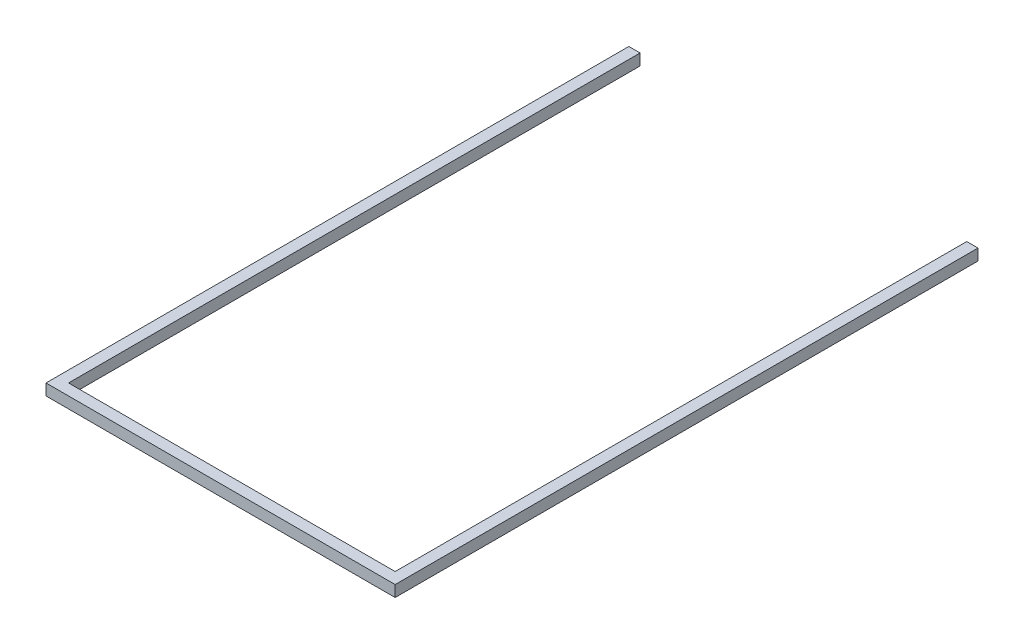
SolidWorks part; units mm, degrees
ref_plane "Front Plane" through (0, 0, 0) normal (0, 0, 1) x (1, 0, 0)
ref_plane "Top Plane" through (0, 0, 0) normal (0, 1, 0) x (1, 0, 0)
ref_plane "Right Plane" through (0, 0, 0) normal (1, 0, 0) x (0, 0, -1)
sketch "Sketch1" plane through (0, 0, 0) normal (0, 1, 0) x (1, 0, 0)
  line L0 (-81.1443, 976.7878) -> (-81.1443, -58.2122)
  line L1 (-81.1443, -58.2122) -> (538.8557, -58.2122)
  line L2 (538.8557, -58.2122) -> (538.8557, 976.7878)
  line L3 (538.8557, 976.7878) -> (518.8557, 976.7878)
  line L4 (518.8557, 976.7878) -> (518.8557, -38.2122)
  line L5 (518.8557, -38.2122) -> (-61.1443, -38.2122)
  line L6 (-61.1443, -38.2122) -> (-61.1443, 976.7878)
  line L7 (-61.1443, 976.7878) -> (-81.1443, 976.7878)
  line L8 (-61.1443, -38.2122) -> (-61.1443, -58.2122) construction
  dimension "D1" = 1035
  dimension "D2" = 20
  dimension "D3" = 620
extrude "Boss-Extrude1" add sketch "Sketch1" along normal blind 20
